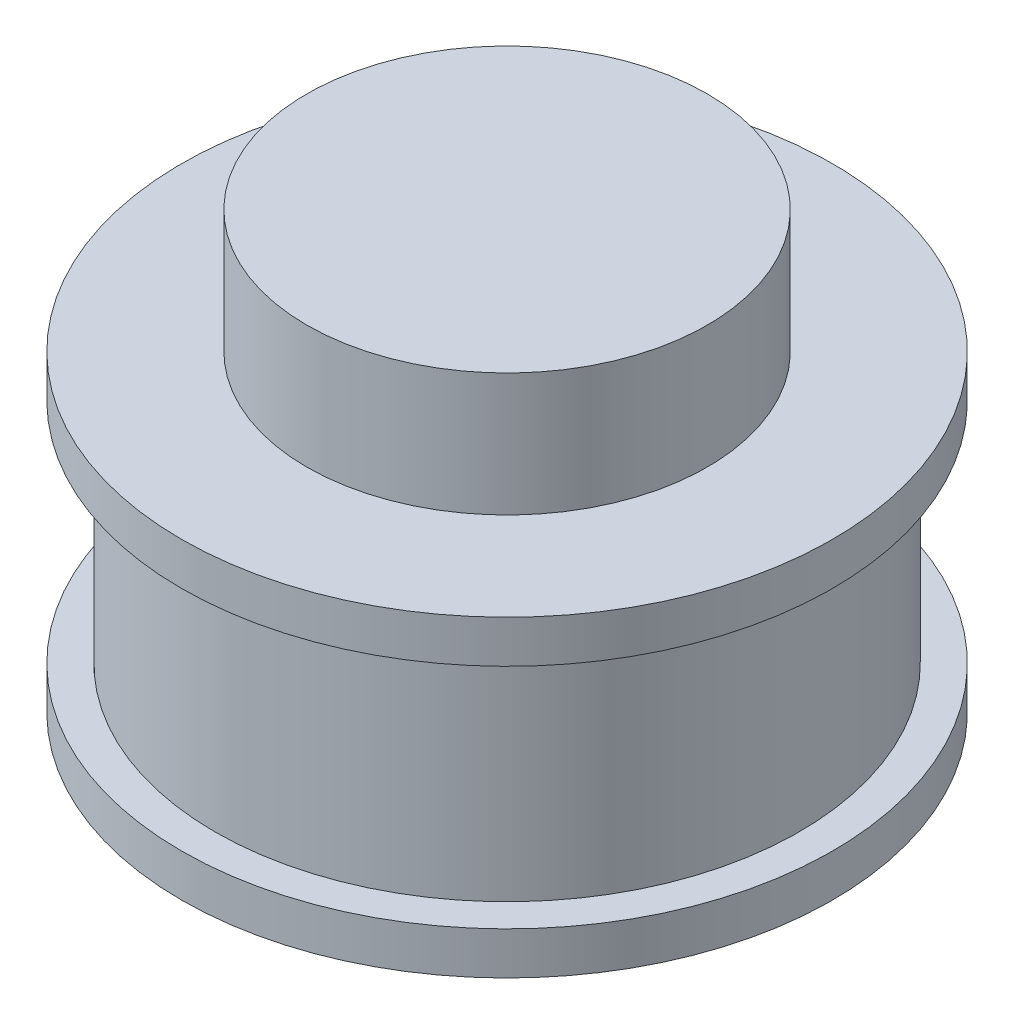
SolidWorks part; units mm, degrees
ref_plane "Front Plane" through (0, 0, 0) normal (0, 0, 1) x (1, 0, 0)
ref_plane "Top Plane" through (0, 0, 0) normal (0, 1, 0) x (1, 0, 0)
ref_plane "Right Plane" through (0, 0, 0) normal (1, 0, 0) x (0, 0, -1)
sketch "Sketch1" plane through (0, 0, 0) normal (0, 0, 1) x (1, 0, 0)
  line L0 (0, 27.6098) -> (0, 0) construction
  line L1 (0, 27.6098) -> (12.7, 27.6098)
  line L2 (0, 0) -> (20.6375, 0)
  line L3 (20.6375, 0) -> (20.6375, 2.6973)
  line L4 (18.5293, 2.6973) -> (18.5293, 17.1147)
  line L5 (18.5293, 9.906) -> (20.6375, 9.906) construction
  line L6 (18.5293, 2.6973) -> (20.6375, 2.6973)
  line L7 (18.5293, 17.1147) -> (20.6375, 17.1147)
  line L8 (20.6375, 19.812) -> (12.7, 19.812)
  line L9 (12.7, 19.812) -> (12.7, 27.6098)
  line L10 (20.6375, 17.1147) -> (20.6375, 19.812)
  line L11 (0, 27.6098) -> (0, 0)
  dimension "D1" = 27.6098
  dimension "D2" = 12.7
  dimension "D3" = 20.6375
  dimension "D4" = 19.812
  dimension "D5" = 18.5293
  dimension "D6" = 17.1147
  dimension "D7" = 17.1147
revolve "Revolve1" add sketch "Sketch1" angle 360 about L11
